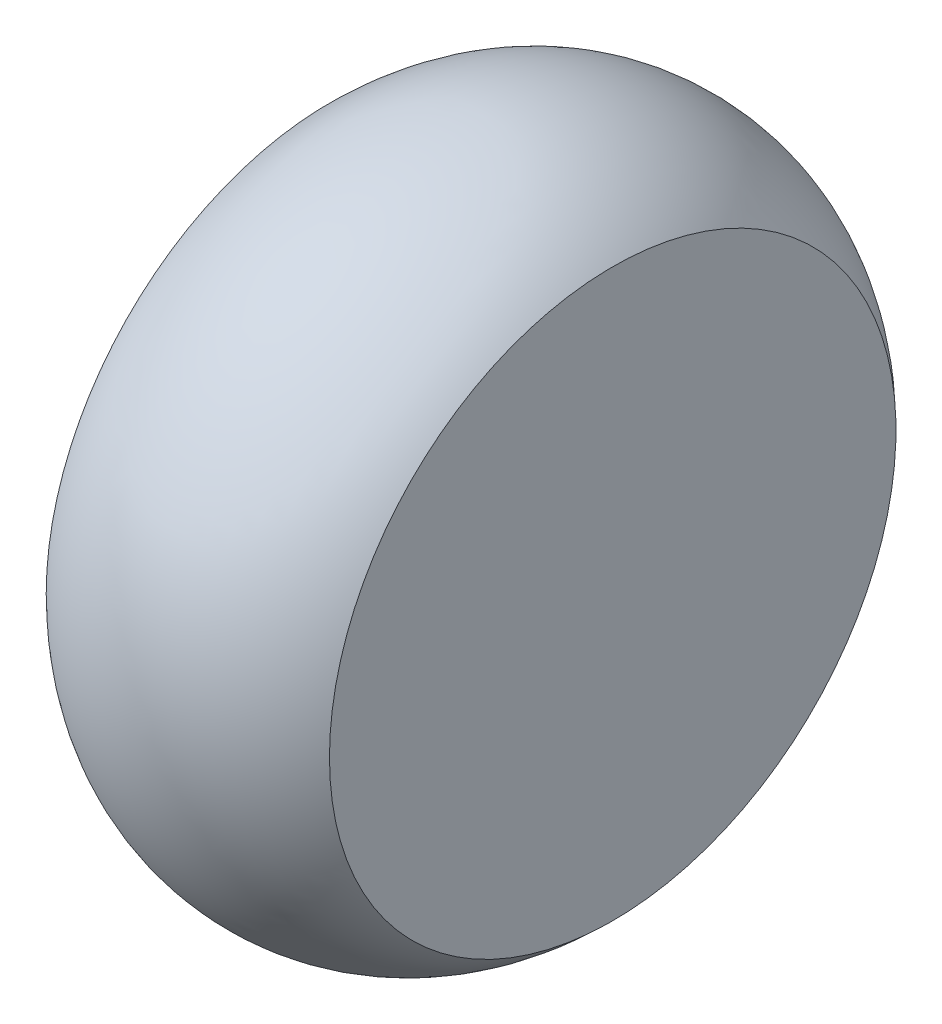
SolidWorks part; units mm, degrees
ref_plane "Front Plane" through (0, 0, 0) normal (0, 0, 1) x (1, 0, 0)
ref_plane "Top Plane" through (0, 0, 0) normal (0, 1, 0) x (1, 0, 0)
ref_plane "Right Plane" through (0, 0, 0) normal (1, 0, 0) x (0, 0, -1)
sketch "Sketch2" plane through (0, 0, 0) normal (1, 0, 0) x (0, 0, -1)
  circle A0 centre (0, 0) radius 40
  circle A1 centre (0, 0) radius 23.2588
  dimension "D1" = 80
extrude "Boss-Extrude1" add sketch "Sketch2" along normal mid plane 40 contours A1 | A0 A1
sketch "Sketch5" plane through (0, 0, 0) normal (0, 0, 1) x (1, 0, 0)
  line L0 (0, 0) -> (42.2046, 0) construction
sketch "Sketch3" plane through (0, 0, 0) normal (0, 0, 1) x (1, 0, 0)
  line L0 (-20, 40) -> (20, 40)
  arc A0 (-20, 40) -> (20, 40) centre (0, 20) cw
revolve "Revolve1" add sketch "Sketch3" angle 360 about L0
